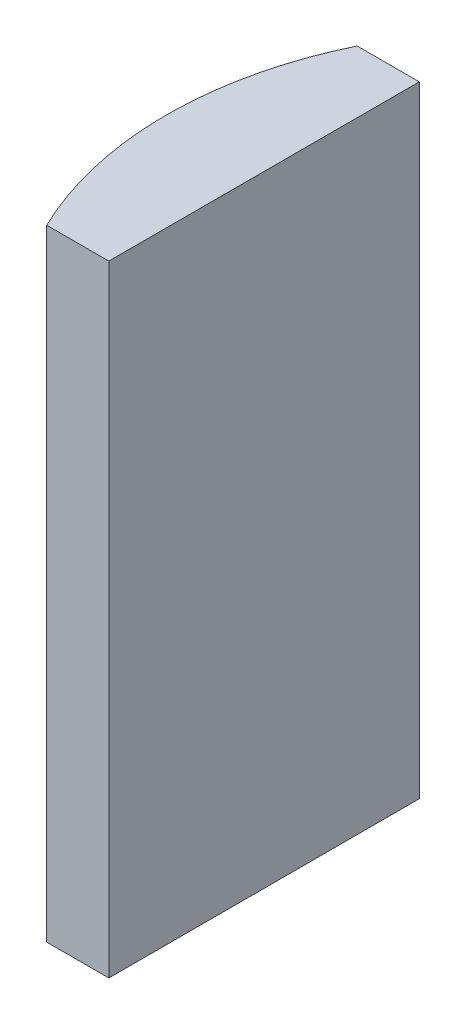
SolidWorks part; units mm, degrees
ref_plane "前视基准面" through (0, 0, 0) normal (0, 0, 1) x (1, 0, 0)
ref_plane "上视基准面" through (0, 0, 0) normal (0, 1, 0) x (1, 0, 0)
ref_plane "右视基准面" through (0, 0, 0) normal (1, 0, 0) x (0, 0, -1)
sketch "草图1" plane through (0, 0, 0) normal (0, 1, 0) x (1, 0, 0)
  line L0 (-137.6835, 0) -> (10.8051, 0) construction
  line L1 (-5.9454, 5) -> (-3.9448, 5)
  line L2 (-5.9454, -5) -> (-3.9448, -5)
  line L3 (-3.9448, 5) -> (-3.9448, -5)
  arc A0 (-5.9454, 5) -> (-5.9454, -5) centre (4.3552, 0) ccw
  point P2 (-7.0948, 0)
  point P4 (-3.9448, 0)
  dimension "D2" = 5
  dimension "D3" = 11.45
  dimension "D4" = 3.15
  dimension "D1" = 5
extrude "凸台-拉伸1" add sketch "草图1" along normal blind 20
